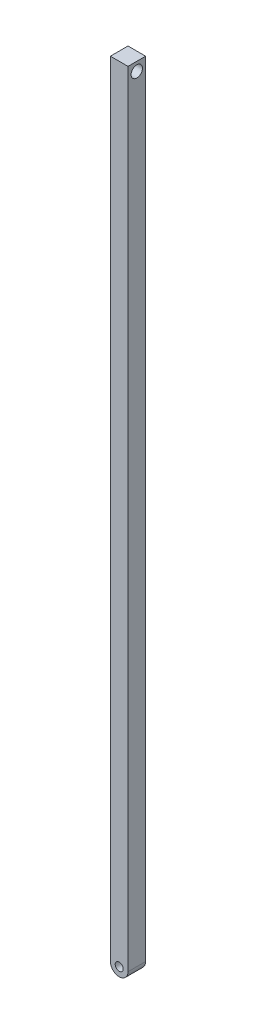
SolidWorks part; units mm, degrees
material "Galvanized Steel"
ref_plane "Front Plane" through (0, 0, 0) normal (0, 0, 1) x (1, 0, 0)
ref_plane "Top Plane" through (0, 0, 0) normal (0, 1, 0) x (1, 0, 0)
ref_plane "Right Plane" through (0, 0, 0) normal (1, 0, 0) x (0, 0, -1)
sketch "Sketch1" plane through (0, 0, 0) normal (0, 0, 1) x (1, 0, 0)
  line L2 (3.4438, -22.2561) -> (3.4438, -66.7561)
  line L4 (4.4438, -66.7561) -> (4.4438, -22.2561)
  line L5 (3.4438, -22.2561) -> (4.4438, -22.2561)
  arc A0 (3.4438, -66.7561) -> (4.4438, -66.7561) centre (3.9438, -66.7561) ccw
  circle A1 centre (3.9438, -66.7561) radius 0.2278
  dimension "D1" = 44.5
extrude "Boss-Extrude1" add sketch "Sketch1" along normal blind 1
sketch "Sketch2" plane through (4.4438, 0, 0) normal (1, 0, 0) x (0, 0, -1)
  line L0 (-0.5, -66.7561) -> (-0.5, -22.7561) construction
  line L1 (-1, -66.7561) -> (0, -66.7561) construction
  circle A0 centre (-0.5, -22.7561) radius 0.3231
  dimension "D1" = 44
extrude "Cut-Extrude1" cut sketch "Sketch2" against normal through all
